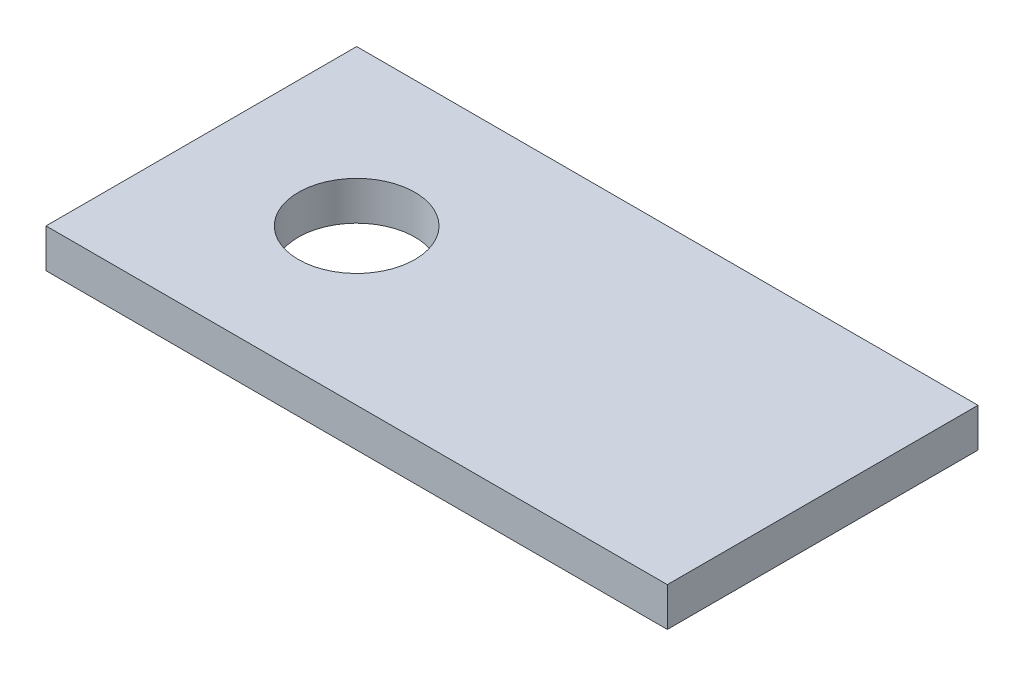
SolidWorks part; units mm, degrees
ref_plane "Front Plane" through (0, 0, 0) normal (0, 0, 1) x (1, 0, 0)
ref_plane "Top Plane" through (0, 0, 0) normal (0, 1, 0) x (1, 0, 0)
ref_plane "Right Plane" through (0, 0, 0) normal (1, 0, 0) x (0, 0, -1)
sketch "Sketch1" plane through (0, 0, 0) normal (0, 1, 0) x (1, 0, 0)
  line L1 (-25.4, 12.7) -> (25.4, 12.7)
  line L2 (-25.4, 12.7) -> (-25.4, -12.7)
  line L3 (-25.4, -12.7) -> (25.4, -12.7)
  line L4 (25.4, 12.7) -> (25.4, -12.7)
  line L5 (-25.4, 12.7) -> (25.4, -12.7) construction
  line L6 (-25.4, -12.7) -> (25.4, 12.7) construction
  point P4 (0, 0)
  dimension "D1" = 50.8
  dimension "D2" = 25.4
extrude "Boss-Extrude1" add sketch "Sketch1" along normal blind 3.175
sketch "Sketch2" plane through (0, 3.175, 0) normal (0, 1, 0) x (1, 0, 0)
  line L0 (-12.7, 12.7) -> (-12.7, -12.7) construction
  line L1 (25.4, 12.7) -> (-25.4, 12.7) construction
  line L2 (-25.4, -12.7) -> (25.4, -12.7) construction
  line L3 (-25.4, 0) -> (25.4, 0) construction
  line L4 (-25.4, 12.7) -> (-25.4, -12.7) construction
  line L5 (25.4, -12.7) -> (25.4, 12.7) construction
  circle A0 centre (-12.7, 0) radius 4.7625
  dimension "D2" = 9.525
  dimension "D1" = 38.1
extrude "Cut-Extrude1" cut sketch "Sketch2" against normal blind 3.175
